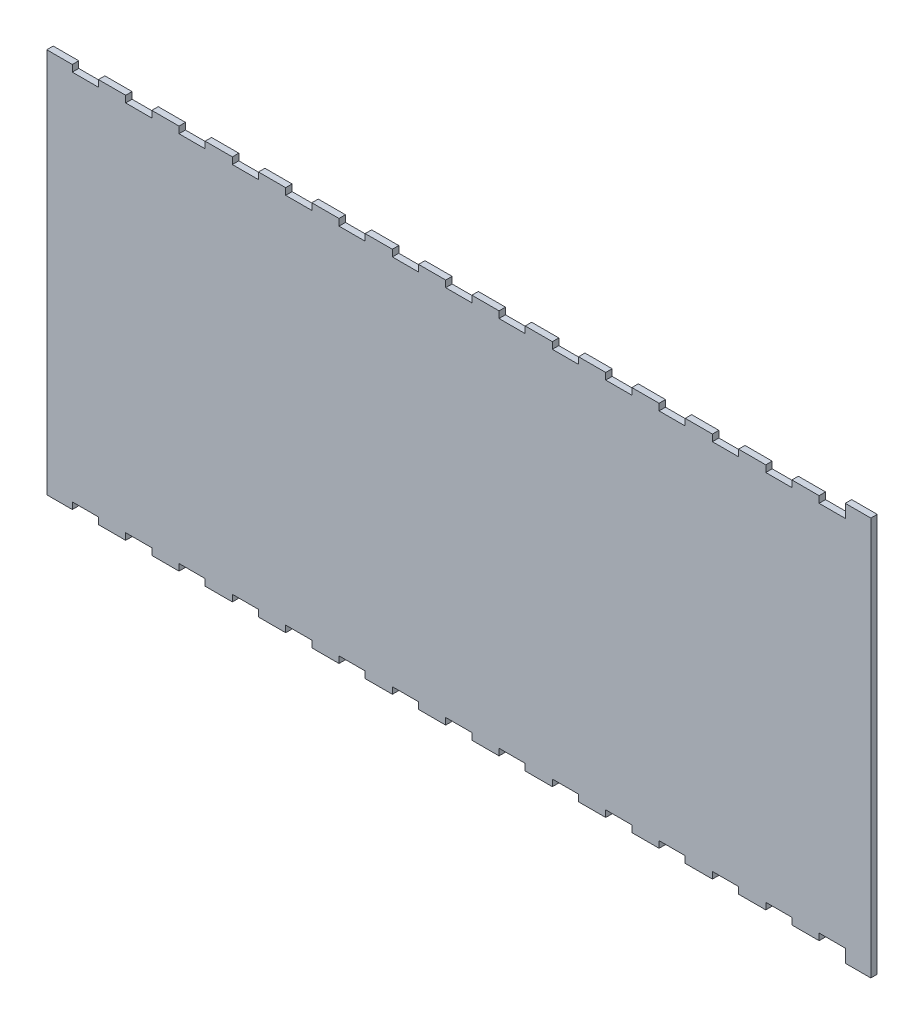
SolidWorks part; units mm, degrees
ref_plane "Front Plane" through (0, 0, 0) normal (0, 0, 1) x (1, 0, 0)
ref_plane "Top Plane" through (0, 0, 0) normal (0, 1, 0) x (1, 0, 0)
ref_plane "Right Plane" through (0, 0, 0) normal (1, 0, 0) x (0, 0, -1)
sketch "Sketch1" plane through (0, 0, 0) normal (0, 0, 1) x (1, 0, 0)
  line L248 (-12.6, 186.8186) -> (-25.5, 186.8186)
  line L249 (-25.5, 186.8186) -> (-25.5, 190.0936)
  line L250 (-25.5, 190.0936) -> (-38.9071, 190.0936)
  line L251 (-38.9071, 190.0936) -> (-38.9071, 186.8186)
  line L252 (-38.9071, 186.8186) -> (-51.8071, 186.8186)
  line L253 (-51.8071, 186.8186) -> (-51.8071, 190.0936)
  line L254 (-51.8071, 190.0936) -> (-65.2143, 190.0936)
  line L255 (-65.2143, 190.0936) -> (-65.2143, 186.8186)
  line L256 (-65.2143, 186.8186) -> (-78.1143, 186.8186)
  line L257 (-78.1143, 186.8186) -> (-78.1143, 190.0936)
  line L258 (-78.1143, 190.0936) -> (-91.5214, 190.0936)
  line L259 (-91.5214, 190.0936) -> (-91.5214, 186.8186)
  line L260 (-91.5214, 186.8186) -> (-104.4214, 186.8186)
  line L261 (-104.4214, 186.8186) -> (-104.4214, 190.0936)
  line L262 (-104.4214, 190.0936) -> (-117.8286, 190.0936)
  line L263 (-117.8286, 190.0936) -> (-117.8286, 186.8186)
  line L264 (-117.8286, 186.8186) -> (-130.7286, 186.8186)
  line L265 (-130.7286, 186.8186) -> (-130.7286, 190.0936)
  line L266 (-130.7286, 190.0936) -> (-144.1357, 190.0936)
  line L267 (-144.1357, 190.0936) -> (-144.1357, 186.8186)
  line L268 (-144.1357, 186.8186) -> (-157.0357, 186.8186)
  line L269 (-157.0357, 186.8186) -> (-157.0357, 190.0936)
  line L270 (-157.0357, 190.0936) -> (-170.4429, 190.0936)
  line L271 (-170.4429, 190.0936) -> (-170.4429, 186.8186)
  line L272 (-170.4429, 186.8186) -> (-183.3429, 186.8186)
  line L273 (-183.3429, 186.8186) -> (-183.3429, 190.0936)
  line L274 (-183.3429, 190.0936) -> (-196.75, 190.0936)
  line L275 (-196.75, 190.0936) -> (-196.75, 186.8186)
  line L276 (-196.75, 186.8186) -> (-209.65, 186.8186)
  line L277 (-209.65, 186.8186) -> (-209.65, 190.0936)
  line L278 (-209.65, 190.0936) -> (-223.0571, 190.0936)
  line L279 (-223.0571, 190.0936) -> (-223.0571, 186.8186)
  line L280 (-223.0571, 186.8186) -> (-235.9571, 186.8186)
  line L281 (-235.9571, 186.8186) -> (-235.9571, 190.0936)
  line L282 (-235.9571, 190.0936) -> (-249.3643, 190.0936)
  line L283 (-249.3643, 190.0936) -> (-249.3643, 186.8186)
  line L284 (-249.3643, 186.8186) -> (-262.2643, 186.8186)
  line L285 (-262.2643, 186.8186) -> (-262.2643, 190.0936)
  line L286 (-262.2643, 190.0936) -> (-275.6714, 190.0936)
  line L287 (-275.6714, 190.0936) -> (-275.6714, 186.8186)
  line L288 (-275.6714, 186.8186) -> (-288.5714, 186.8186)
  line L289 (-288.5714, 186.8186) -> (-288.5714, 190.0936)
  line L290 (-288.5714, 190.0936) -> (-301.9786, 190.0936)
  line L291 (-301.9786, 190.0936) -> (-301.9786, 186.8186)
  line L292 (-301.9786, 186.8186) -> (-314.8786, 186.8186)
  line L293 (-314.8786, 186.8186) -> (-314.8786, 190.0936)
  line L294 (-314.8786, 190.0936) -> (-328.2857, 190.0936)
  line L295 (-328.2857, 190.0936) -> (-328.2857, 186.8186)
  line L296 (-328.2857, 186.8186) -> (-341.1857, 186.8186)
  line L297 (-341.1857, 186.8186) -> (-341.1857, 190.0936)
  line L298 (-341.1857, 190.0936) -> (-354.5929, 190.0936)
  line L299 (-354.5929, 190.0936) -> (-354.5929, 186.8186)
  line L300 (-354.5929, 186.8186) -> (-367.4929, 186.8186)
  line L301 (-367.4929, 186.8186) -> (-367.4929, 190.0936)
  line L302 (-367.4929, 190.0936) -> (-380.9, 190.0936)
  line L303 (-380.9, 190.0936) -> (-380.9, 186.8186)
  line L304 (-380.9, 186.8186) -> (-393.8, 186.8186)
  line L305 (-393.8, 186.8186) -> (-393.8, 190.0936)
  line L306 (-393.8, 190.0936) -> (-406.4, 190.0936)
  line L307 (-406.4, 190.0936) -> (-406.4, 0)
  line L308 (-406.4, 0) -> (-393.8, 0)
  line L309 (-393.8, 0) -> (-393.8, 3.275)
  line L310 (-393.8, 3.275) -> (-380.9, 3.275)
  line L311 (-380.9, 3.275) -> (-380.9, 0)
  line L312 (-380.9, 0) -> (-367.4929, 0)
  line L313 (-367.4929, 0) -> (-367.4929, 3.275)
  line L314 (-367.4929, 3.275) -> (-354.5929, 3.275)
  line L315 (-354.5929, 3.275) -> (-354.5929, 0)
  line L316 (-354.5929, 0) -> (-341.1857, 0)
  line L317 (-341.1857, 0) -> (-341.1857, 3.275)
  line L318 (-341.1857, 3.275) -> (-328.2857, 3.275)
  line L319 (-328.2857, 3.275) -> (-328.2857, 0)
  line L320 (-328.2857, 0) -> (-314.8786, 0)
  line L321 (-314.8786, 0) -> (-314.8786, 3.275)
  line L322 (-314.8786, 3.275) -> (-301.9786, 3.275)
  line L323 (-301.9786, 3.275) -> (-301.9786, 0)
  line L324 (-301.9786, 0) -> (-288.5714, 0)
  line L325 (-288.5714, 0) -> (-288.5714, 3.275)
  line L326 (-288.5714, 3.275) -> (-275.6714, 3.275)
  line L327 (-275.6714, 3.275) -> (-275.6714, 0)
  line L328 (-275.6714, 0) -> (-262.2643, 0)
  line L329 (-262.2643, 0) -> (-262.2643, 3.275)
  line L330 (-262.2643, 3.275) -> (-249.3643, 3.275)
  line L331 (-249.3643, 3.275) -> (-249.3643, 0)
  line L332 (-249.3643, 0) -> (-235.9571, 0)
  line L333 (-235.9571, 0) -> (-235.9571, 3.275)
  line L334 (-235.9571, 3.275) -> (-223.0571, 3.275)
  line L335 (-223.0571, 3.275) -> (-223.0571, 0)
  line L336 (-223.0571, 0) -> (-209.65, 0)
  line L337 (-209.65, 0) -> (-209.65, 3.275)
  line L338 (-209.65, 3.275) -> (-196.75, 3.275)
  line L339 (-196.75, 3.275) -> (-196.75, 0)
  line L340 (-196.75, 0) -> (-183.3429, 0)
  line L341 (-183.3429, 0) -> (-183.3429, 3.275)
  line L342 (-183.3429, 3.275) -> (-170.4429, 3.275)
  line L343 (-170.4429, 3.275) -> (-170.4429, 0)
  line L344 (-170.4429, 0) -> (-157.0357, 0)
  line L345 (-157.0357, 0) -> (-157.0357, 3.275)
  line L346 (-157.0357, 3.275) -> (-144.1357, 3.275)
  line L347 (-144.1357, 3.275) -> (-144.1357, 0)
  line L348 (-144.1357, 0) -> (-130.7286, 0)
  line L349 (-130.7286, 0) -> (-130.7286, 3.275)
  line L350 (-130.7286, 3.275) -> (-117.8286, 3.275)
  line L351 (-117.8286, 3.275) -> (-117.8286, 0)
  line L352 (-117.8286, 0) -> (-104.4214, 0)
  line L353 (-104.4214, 0) -> (-104.4214, 3.275)
  line L354 (-104.4214, 3.275) -> (-91.5214, 3.275)
  line L355 (-91.5214, 3.275) -> (-91.5214, 0)
  line L356 (-91.5214, 0) -> (-78.1143, 0)
  line L357 (-78.1143, 0) -> (-78.1143, 3.275)
  line L358 (-78.1143, 3.275) -> (-65.2143, 3.275)
  line L359 (-65.2143, 3.275) -> (-65.2143, 0)
  line L360 (-65.2143, 0) -> (-51.8071, 0)
  line L361 (-51.8071, 0) -> (-51.8071, 3.275)
  line L362 (-51.8071, 3.275) -> (-38.9071, 3.275)
  line L363 (-38.9071, 3.275) -> (-38.9071, 0)
  line L364 (-38.9071, 0) -> (-25.5, 0)
  line L365 (-25.5, 0) -> (-25.5, 3.275)
  line L366 (-25.5, 3.275) -> (-12.6, 3.275)
  line L367 (-12.6, 3.275) -> (-12.6, -3.175)
  line L368 (-12.6, -3.175) -> (0, -3.175)
  line L369 (0, -3.175) -> (0, 193.2686)
  line L370 (0, 193.2686) -> (-12.6, 193.2686)
  line L371 (-12.6, 193.2686) -> (-12.6, 186.8186)
extrude "Boss-Extrude1" add sketch "Sketch1" along normal blind 3.175
